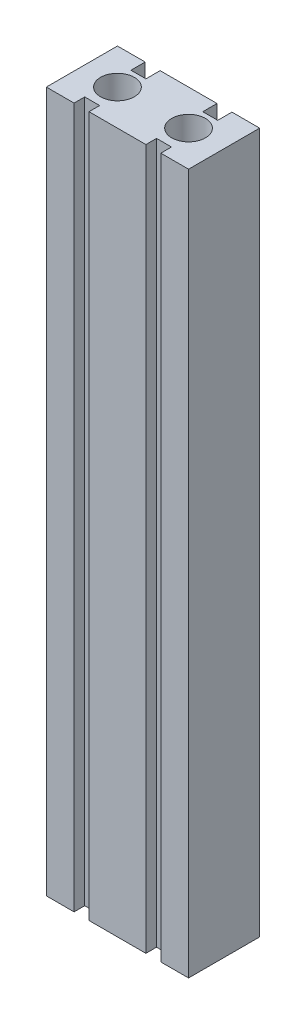
SolidWorks part; units mm, degrees
ref_plane "前视基准面" through (0, 0, 0) normal (0, 0, 1) x (1, 0, 0)
ref_plane "上视基准面" through (0, 0, 0) normal (0, 1, 0) x (1, 0, 0)
ref_plane "右视基准面" through (0, 0, 0) normal (1, 0, 0) x (0, 0, -1)
sketch "草图2" plane through (0, 0, 0) normal (0, 1, 0) x (1, 0, 0)
  line L1 (-20, 10) -> (20, 10)
  line L2 (-20, 10) -> (-20, -10)
  line L3 (-20, -10) -> (20, -10)
  line L4 (20, 10) -> (20, -10)
  line L5 (-20, 10) -> (20, -10) construction
  line L6 (-20, -10) -> (20, 10) construction
  point P0 (0, 0)
  dimension "D1" = 40
  dimension "D2" = 20
extrude "凸台-拉伸1" add sketch "草图2" along normal blind 197
sketch "草图3" plane through (0, 0, 0) normal (0, -1, 0) x (1, 0, 0)
  line L0 (0, 0) -> (0, -14.1253) construction
  line L2 (20, -10) -> (-20, -10) construction
  circle A0 centre (-10, 0) radius 4.75
  circle A1 centre (10, 0) radius 4.75
  point P7 (0, 0)
  dimension "D2" = 9.5
  dimension "D1" = 20
  dimension "D3" = 10
extrude "切除-拉伸1" cut sketch "草图3" against normal through all
sketch "草图4" plane through (0, 0, 10) normal (0, 0, 1) x (1, 0, 0)
  line L0 (0, 0) -> (0, 202.505) construction
  line L1 (-20, 0) -> (20, 0) construction
  line L2 (-12.2, 0) -> (-8, 0)
  line L3 (-12.2, 0) -> (-12.2, 197)
  line L4 (-12.2, 197) -> (-8, 197)
  line L5 (-8, 0) -> (-8, 197)
  line L6 (-20, 197) -> (20, 197) construction
  line L7 (12.2, 0) -> (8, 0)
  line L8 (12.2, 197) -> (8, 197)
  line L9 (8, 0) -> (8, 197)
  line L10 (12.2, 0) -> (12.2, 197)
  dimension "D1" = 4.2
  dimension "D2" = 16
extrude "切除-拉伸2" cut sketch "草图4" against normal blind 3
sketch "草图5" plane through (0, 0, -10) normal (0, 0, -1) x (-1, 0, 0)
  line L4 (-12.2, 0) -> (-8, 0)
  line L5 (-8, 0) -> (-8, 197)
  line L6 (-8, 197) -> (-12.2, 197)
  line L7 (-12.2, 197) -> (-12.2, 0)
  line L8 (-12.2, 0) -> (-8, 0)
  line L9 (-8, 0) -> (-8, 197)
  line L10 (-8, 197) -> (-12.2, 197)
  line L11 (-12.2, 197) -> (-12.2, 0)
  line L12 (8, 0) -> (12.2, 0)
  line L13 (8, 197) -> (8, 0)
  line L14 (12.2, 197) -> (8, 197)
  line L15 (12.2, 0) -> (12.2, 197)
  line L16 (8, 0) -> (12.2, 0)
  line L17 (8, 197) -> (8, 0)
  line L18 (12.2, 197) -> (8, 197)
  line L19 (12.2, 0) -> (12.2, 197)
  dimension "D1" = 0
  dimension "D2" = 0
extrude "切除-拉伸3" cut sketch "草图5" against normal blind 4
